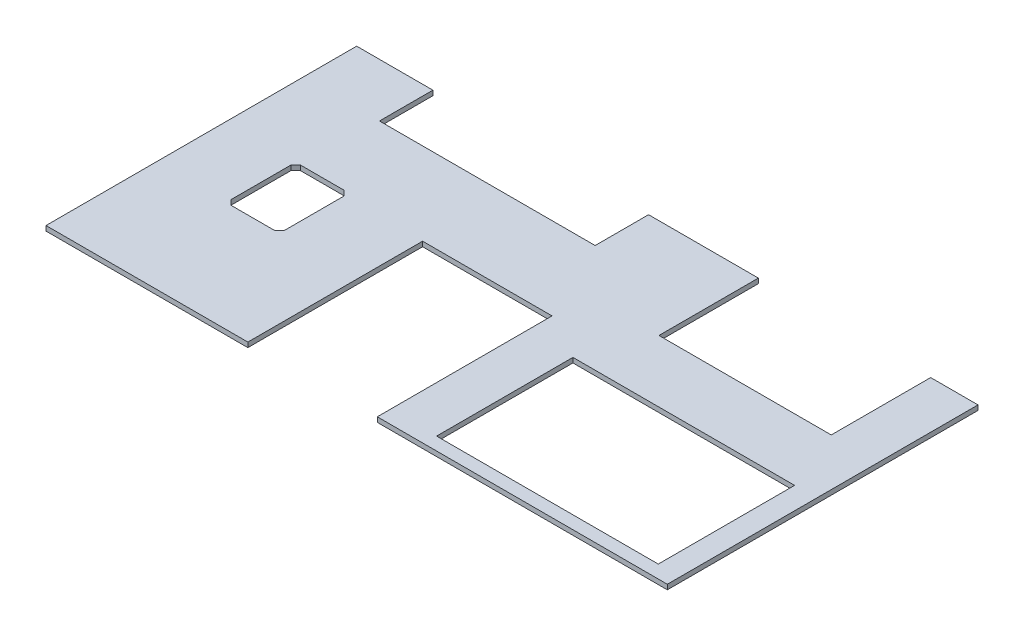
SolidWorks part; units mm, degrees
material "Oak"
ref_plane "Front Plane" through (0, 0, 0) normal (0, 0, 1) x (1, 0, 0)
ref_plane "Top Plane" through (0, 0, 0) normal (0, 1, 0) x (1, 0, 0)
ref_plane "Right Plane" through (0, 0, 0) normal (1, 0, 0) x (0, 0, -1)
sketch "Sketch1" plane through (0, 0, 0) normal (0, 1, 0) x (1, 0, 0)
  line L4 (2438.4, 0) -> (2438.4, 1219.2)
  line L5 (2438.4, 1219.2) -> (0, 1219.2)
  line L7 (0, 0) -> (2438.4, 0)
  line L8 (0, 1219.2) -> (0, 0)
  dimension "D1" = 2438.4
  dimension "D5" = 1219.2
extrude "Boss-Extrude1" add sketch "Sketch1" against normal blind 19.05
sketch "Sketch2" plane through (0, 0, 0) normal (0, 1, 0) x (1, 0, 0)
  line L1 (1482.09, 585.7875) -> (2352.04, 585.7875)
  line L2 (1482.09, 585.7875) -> (1482.09, 50.8)
  line L3 (1482.09, 50.8) -> (2352.04, 50.8)
  line L4 (2352.04, 585.7875) -> (2352.04, 50.8)
  dimension "D1" = 869.95
  dimension "D2" = 534.9875
  dimension "D3" = 1482.09
  dimension "D4" = 50.8
extrude "Cut-Extrude1" cut sketch "Sketch2" against normal through all
sketch "Sketch3" plane through (0, 0, 0) normal (0, 1, 0) x (1, 0, 0)
  line L0 (0, 0) -> (2438.4, 0) construction
  line L1 (792.1625, 685.8) -> (1300.1625, 685.8)
  line L2 (792.1625, 685.8) -> (792.1625, 0)
  line L3 (792.1625, 0) -> (1300.1625, 0)
  line L4 (1300.1625, 685.8) -> (1300.1625, 0)
  dimension "D1" = 508
  dimension "D2" = 792.1625
  dimension "D3" = 685.8
extrude "Cut-Extrude2" cut sketch "Sketch3" against normal through all
sketch "Sketch4" plane through (0, 0, 0) normal (0, 1, 0) x (1, 0, 0)
  line L1 (1576.4256, 1692.91) -> (2252.6269, 1692.91)
  line L2 (1576.4256, 1692.91) -> (1576.4256, 829.0585)
  line L3 (1576.4256, 829.0585) -> (2252.6269, 829.0585)
  line L4 (2252.6269, 1692.91) -> (2252.6269, 829.0585)
  dimension "D1" = 1576.4256
  dimension "D2" = 676.2013
  dimension "D3" = 1692.91
  dimension "D4" = 863.8515
extrude "Cut-Extrude3" cut sketch "Sketch4" against normal through all
sketch "Sketch5" plane through (0, 0, 0) normal (0, 1, 0) x (1, 0, 0)
  line L1 (299.1104, 1219.2) -> (1145.54, 1219.2)
  line L2 (299.1104, 1219.2) -> (299.1104, 1012.825)
  line L3 (299.1104, 1012.825) -> (1145.54, 1012.825)
  line L4 (1145.54, 1219.2) -> (1145.54, 1012.825)
  line L7 (2438.4, 1219.2) -> (2252.6269, 1219.2) construction
  dimension "D1" = 299.1104
  dimension "D2" = 846.4296
  dimension "D3" = 1012.825
extrude "Cut-Extrude4" cut sketch "Sketch5" against normal through all
sketch "Sketch8" plane through (0, 0, 0) normal (0, 1, 0) x (1, 0, 0)
  line L0 (294.0685, 704.85) -> (275.0185, 685.8)
  line L1 (294.0685, 704.85) -> (465.5185, 704.85)
  line L2 (275.0185, 685.8) -> (275.0185, 450.85)
  line L3 (294.0685, 431.8) -> (465.5185, 431.8)
  line L4 (484.5685, 685.8) -> (484.5685, 450.85)
  line L5 (379.7935, 369.414) -> (379.7935, 778.191) construction
  line L6 (219.5895, 568.325) -> (559.0988, 568.325) construction
  line L7 (465.5185, 704.85) -> (484.5685, 685.8)
  line L8 (465.5185, 431.8) -> (484.5685, 450.85)
  line L9 (294.0685, 431.8) -> (275.0185, 450.85)
  point P4 (379.7935, 704.85)
  dimension "D5" = 19.05
  dimension "D1" = 275.0185
  dimension "D2" = 209.55
  dimension "D3" = 431.8
  dimension "D4" = 273.05
  dimension "D6" = 19.05
extrude "Cut-Extrude6" cut sketch "Sketch8" against normal through all
sketch "Sketch9" plane through (299.1104, 0, 0) normal (-1, 0, 0) x (0, 0, 1)
  line L4 (0, 0) -> (-1219.2, 0)
  line L5 (-1219.2, 0) -> (-1219.2, -19.05)
  line L6 (-1219.2, -19.05) -> (0, -19.05)
  line L7 (0, -19.05) -> (0, 0)
  line L8 (-1009.6018, 0) -> (-1219.2, 0)
  line L9 (-1219.2, 0) -> (-1219.2, -19.05)
  line L10 (-1219.2, -19.05) -> (-1005.2932, -19.05)
  arc A1 (-1005.2932, -19.05) -> (-1009.6018, 0) centre (-1430.274, -105.156) ccw
  point P4 (0, 0)
  point P5 (0, 0)
  point P6 (-1012.825, 22.7078)
  dimension "D3" = 433.6161
  dimension "D1" = 1430.274
  dimension "D2" = 105.156
  dimension "D4" = 0
extrude "Cut-Extrude7" cut sketch "Sketch9" against normal up to surface (846.4296 mm away) up to face at (1145.54, -9.525, -1116.0125)
